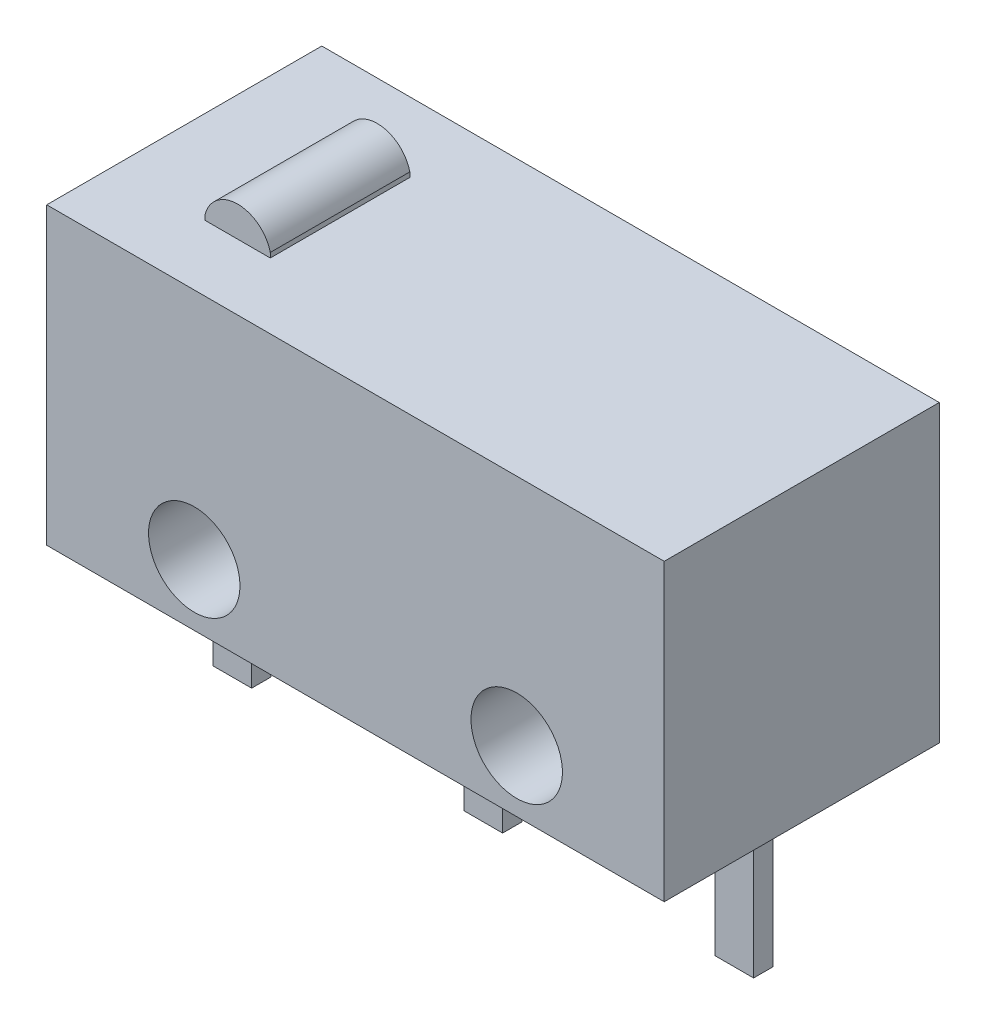
SolidWorks part; units mm, degrees
ref_plane "Front" through (0, 0, 0) normal (0, 0, 1) x (1, 0, 0)
ref_plane "Top" through (0, 0, 0) normal (0, 1, 0) x (1, 0, 0)
ref_plane "Right" through (0, 0, 0) normal (1, 0, 0) x (0, 0, -1)
ref_plane "Plane1" through (3.15, 0, 0) normal (1, 0, 0) x (0, 0, -1)
sketch "Sketch1" plane through (3.15, 0, 0) normal (1, 0, 0) x (0, 0, -1)
  line L0 (2.9, -1.5) -> (2.9, 4.627)
  line L1 (2.9, 4.627) -> (-2.815, 4.627)
  line L2 (-2.815, 4.627) -> (-2.815, -1.5)
  line L3 (-2.815, -1.5) -> (2.9, -1.5)
  dimension "D1" = 6.127
  dimension "D2" = 5.715
extrude "Extrude1" add sketch "Sketch1" against normal blind 12.83
sketch "Sketch2" plane through (0, 0, 2.815) normal (0, 0, 1) x (1, 0, 0)
  line L0 (-9.68, -1.5) -> (3.15, -1.5) construction
  line L3 (-3.265, -1.5) -> (-3.265, 4.627) construction
  line L4 (-9.68, 4.627) -> (3.15, 4.627) construction
  circle A0 centre (0.085, -0.223) radius 0.95
  circle A2 centre (-6.615, -0.223) radius 0.95
  dimension "D3" = 1.9
  dimension "D2" = 6.7
  dimension "D1" = 4.85
extrude "Cut-Extrude1" cut sketch "Sketch2" against normal blind 20.8
sketch "Sketch4" plane through (0, -1.5, 0) normal (0, -1, 0) x (1, 0, 0)
  line L0 (-8.08, 0.1575) -> (-8.08, -0.2425)
  line L1 (-8.08, -0.2425) -> (-8.88, -0.2425)
  line L2 (-8.88, -0.2425) -> (-8.88, 0.1575)
  line L3 (-8.88, 0.1575) -> (-8.08, 0.1575)
  line L4 (-2.865, 0.1575) -> (-2.865, -0.2425)
  line L5 (-9.68, 2.815) -> (3.15, 2.815) construction
  line L6 (-3.265, 2.815) -> (-3.265, -2.9) construction
  line L7 (-9.68, -2.9) -> (3.15, -2.9) construction
  line L8 (2.35, 0.1575) -> (1.55, 0.1575)
  line L9 (2.35, -0.2425) -> (2.35, 0.1575)
  line L10 (1.55, -0.2425) -> (2.35, -0.2425)
  line L11 (1.55, 0.1575) -> (1.55, -0.2425)
  line L12 (-2.865, -0.2425) -> (-3.665, -0.2425)
  line L13 (-3.665, -0.2425) -> (-3.665, 0.1575)
  line L14 (-3.665, 0.1575) -> (-2.865, 0.1575)
  line L15 (-9.68, 2.815) -> (-9.68, -2.9) construction
  line L16 (-3.265, 0.1575) -> (-3.265, -0.2425) construction
  line L17 (-9.68, -0.0425) -> (3.15, -0.0425) construction
  line L18 (3.15, 2.815) -> (3.15, -2.9) construction
  line L19 (-8.88, -0.0425) -> (-8.08, -0.0425) construction
  line L20 (-8.48, 0.1575) -> (-8.48, -0.2425) construction
  line L21 (-3.265, -0.2425) -> (-3.665, -0.0425) construction
  line L22 (-3.665, -0.0425) -> (-2.865, -0.0425) construction
  dimension "D1" = 0.8
  dimension "D2" = 0.4
  dimension "D3" = 0.8
  dimension "D4" = 0.4
  dimension "D5" = 0.8
  dimension "D6" = 0.8
extrude "Extrude2" add sketch "Sketch4" along normal blind 3.1
ref_plane "Plane2" through (0, 0, -1.45) normal (0, 0, -1) x (-1, 0, 0)
sketch "Sketch7" plane through (0, 0, -1.45) normal (0, 0, -1) x (-1, 0, 0)
  line L0 (7.7557, 4.627) -> (6.4002, 4.627)
  line L1 (9.68, 4.627) -> (-3.15, 4.627) construction
  line L3 (7.7557, 4.627) -> (7.7557, 4.727)
  line L4 (6.4002, 4.627) -> (6.4002, 4.727)
  arc A1 (6.4002, 4.727) -> (7.7557, 4.727) centre (7.0779, 4.5615) cw
  dimension "D1" = 0.1
extrude "Extrude5" add sketch "Sketch7" against normal blind 2.9
